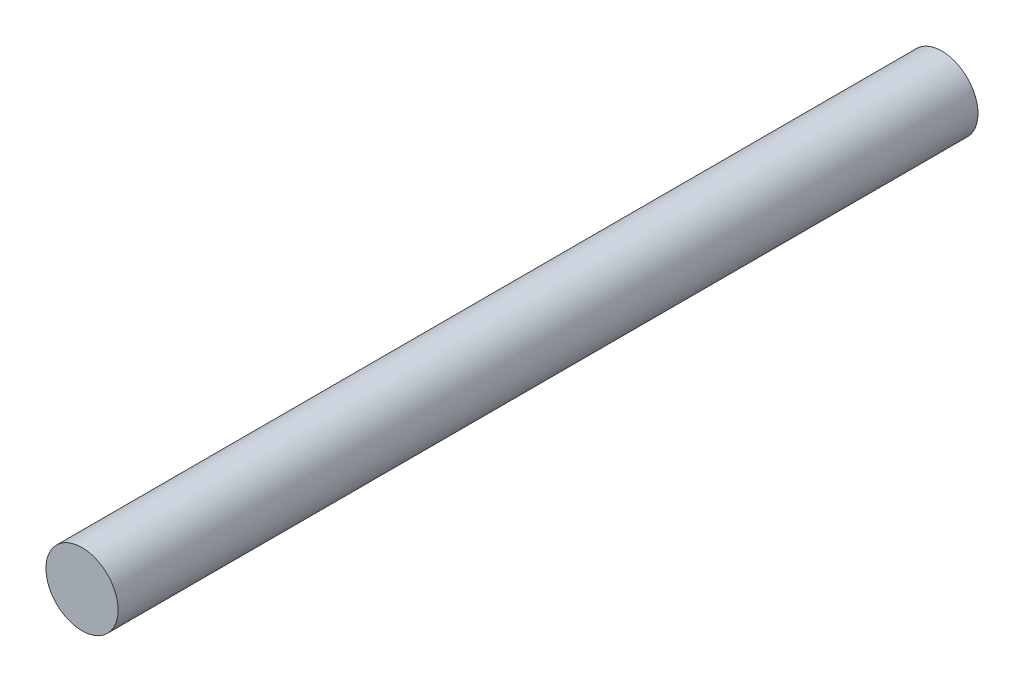
SolidWorks part; units mm, degrees
ref_plane "Front Plane" through (0, 0, 0) normal (0, 0, 1) x (1, 0, 0)
ref_plane "Top Plane" through (0, 0, 0) normal (0, 1, 0) x (1, 0, 0)
ref_plane "Right Plane" through (0, 0, 0) normal (1, 0, 0) x (0, 0, -1)
sketch "Sketch1" plane through (0, 0, 0) normal (0, 0, 1) x (1, 0, 0)
  circle A0 centre (0, 0) radius 4.2625
  dimension "D1" = 8.525
extrude "Boss-Extrude1" add sketch "Sketch1" along normal blind 101.6
